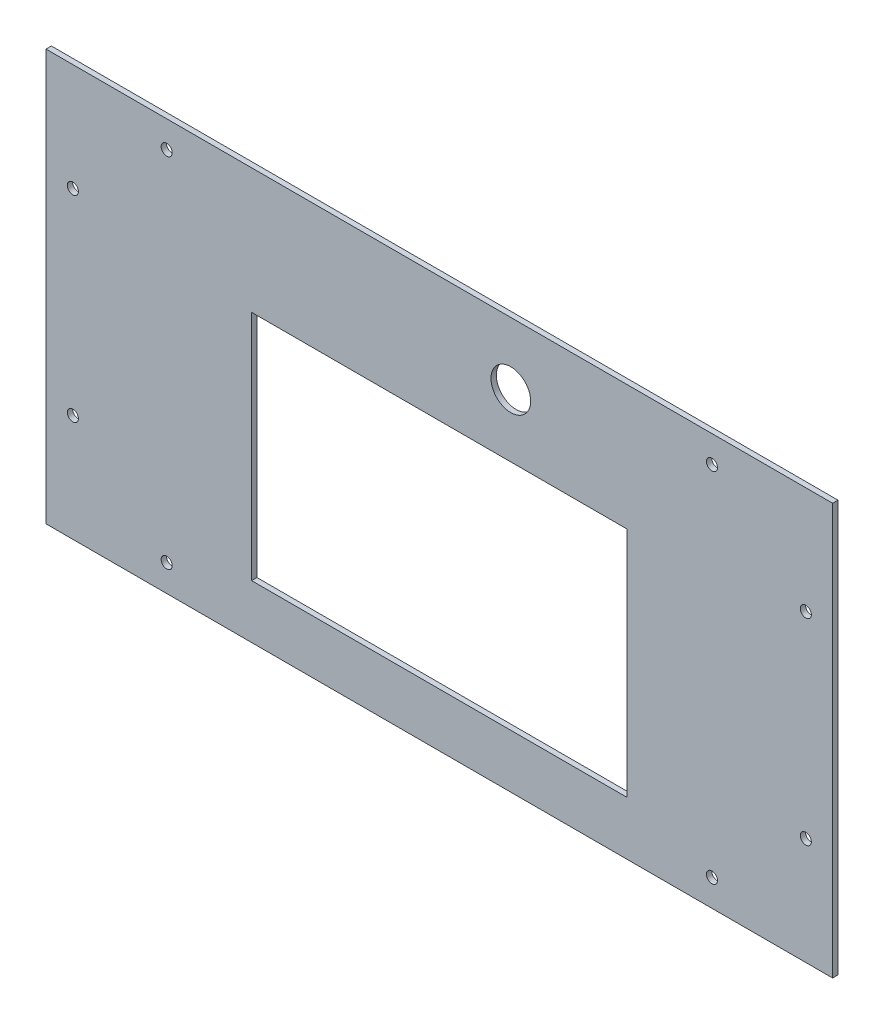
SolidWorks part; units mm, degrees
ref_plane "Alzado" through (0, 0, 0) normal (0, 0, 1) x (1, 0, 0)
ref_plane "Planta" through (0, 0, 0) normal (0, 1, 0) x (1, 0, 0)
ref_plane "Vista lateral" through (0, 0, 0) normal (1, 0, 0) x (0, 0, -1)
sketch "Croquis1" plane through (0, 0, 0) normal (0, 0, 1) x (1, 0, 0)
  line L0 (0, 0) -> (0, 50000) construction
  line L1 (-220, 115) -> (220, 115)
  line L2 (-220, 115) -> (-220, -115)
  line L3 (-220, -115) -> (220, -115)
  line L4 (220, 115) -> (220, -115)
  line L5 (-220, 115) -> (220, -115) construction
  line L6 (-220, -115) -> (220, 115) construction
  line L7 (-120, 238.6287) -> (-120, -49761.3713) construction
  line L8 (-180, -189.4992) -> (-180, 49810.5008) construction
  line L9 (-205, 115) -> (-205, -115) construction
  line L10 (-220, 100) -> (220, 100) construction
  line L11 (0, 0) -> (-50000, 0) construction
  point P0 (0, 0)
  dimension "D1" = 440
  dimension "D2" = 230
  dimension "D3" = 40
  dimension "D4" = 60
  dimension "D5" = 15
  dimension "D6" = 15
extrude "Saliente-Extruir1" add sketch "Croquis1" along normal blind 3
sketch "Croquis2" plane through (0, 0, 3) normal (0, 0, 1) x (1, 0, 0)
  line L0 (-205, 115) -> (-205, -115) construction
  line L1 (-220, 100) -> (220, 100) construction
  line L3 (200000, 0) -> (-250000, 0) construction
  line L4 (0, -200000) -> (0, 250000) construction
  line L5 (200000, 0) -> (-250000, 0) construction
  line L6 (0, -200000) -> (0, 250000) construction
  circle A0 centre (-205, 55) radius 3.1
  circle A2 centre (-152.5, 100) radius 3.1
  circle A4 centre (152.5, 100) radius 3.1
  circle A5 centre (-205, -55) radius 3.1
  circle A6 centre (205, -55) radius 3.1
  circle A7 centre (205, 55) radius 3.1
  circle A8 centre (152.5, -100) radius 3.1
  circle A9 centre (-152.5, -100) radius 3.1
  dimension "D1" = 6.2
  dimension "D2" = 110
  dimension "D3" = 305
extrude "Cortar-Extruir1" cut sketch "Croquis2" against normal through all
sketch "Croquis3" plane through (0, 0, 0) normal (0, 0, -1) x (-1, 0, 0)
  line L1 (-105, 45) -> (105, 45)
  line L2 (-105, 45) -> (-105, -85)
  line L3 (-105, -85) -> (105, -85)
  line L4 (105, 45) -> (105, -85)
  line L5 (-105, 45) -> (105, -85) construction
  line L6 (-105, -85) -> (105, 45) construction
  point P0 (0, -20)
  dimension "D1" = 210
  dimension "D2" = 130
  dimension "D3" = 20
extrude "Cortar-Extruir2" cut sketch "Croquis3" against normal through all
sketch "Croquis4" plane through (0, 0, 0) normal (0, 0, -1) x (-1, 0, 0)
  line L0 (105, 45) -> (-105, 45) construction
  circle A0 centre (-40, 80) radius 11.1
  point P4 (0, 0)
  point P6 (-54.3136, 75)
  dimension "D1" = 22.2
  dimension "D2" = 35
  dimension "D3" = 40
  dimension "D4" = 80
extrude "Cortar-Extruir3" cut sketch "Croquis4" against normal through all
